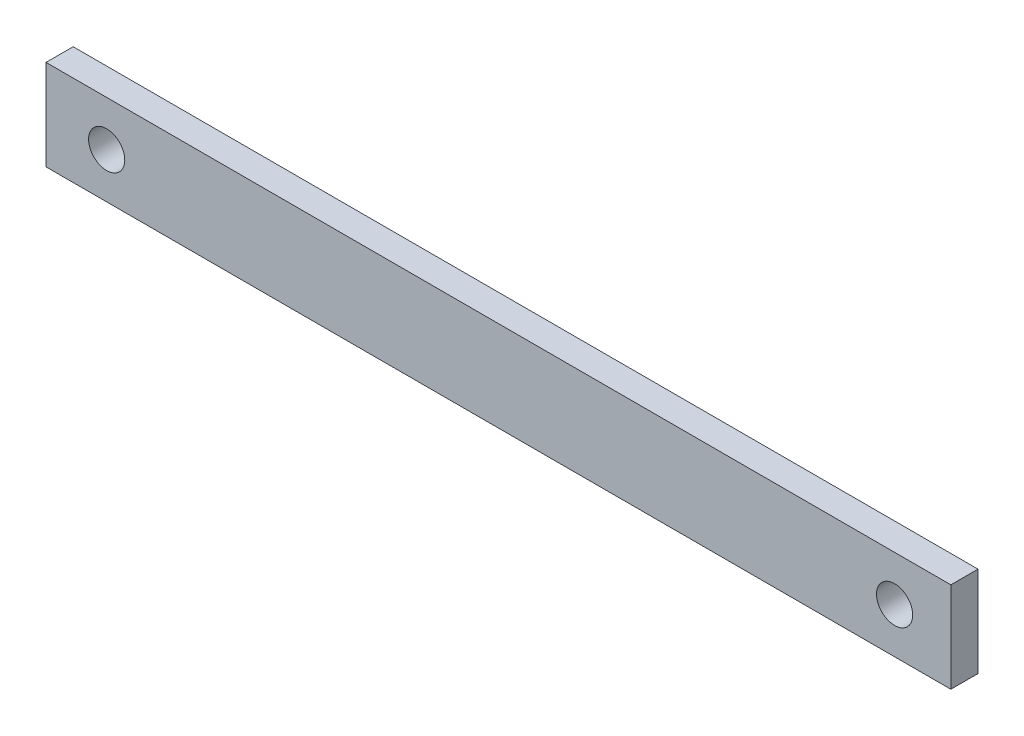
SolidWorks part; units mm, degrees
ref_plane "Front Plane" through (0, 0, 0) normal (0, 0, 1) x (1, 0, 0)
ref_plane "Top Plane" through (0, 0, 0) normal (0, 1, 0) x (1, 0, 0)
ref_plane "Right Plane" through (0, 0, 0) normal (1, 0, 0) x (0, 0, -1)
sketch "Sketch1" plane through (0, 0, 0) normal (0, 0, 1) x (1, 0, 0)
  line L1 (-50, 5) -> (50, 5)
  line L2 (-50, 5) -> (-50, -5)
  line L3 (-50, -5) -> (50, -5)
  line L4 (50, 5) -> (50, -5)
  line L5 (-50, 5) -> (50, -5) construction
  line L6 (-50, -5) -> (50, 5) construction
  point P0 (0, 0)
  dimension "D1" = 100
  dimension "D2" = 10
extrude "Boss-Extrude1" add sketch "Sketch1" along normal blind 3
sketch "Sketch2" plane through (0, 0, 3) normal (0, 0, 1) x (1, 0, 0)
  circle A0 centre (-43.2953, 0) radius 2
  circle A1 centre (43.7829, 0) radius 2
  point P4 (0, 0)
  dimension "D1" = 4
extrude "Cut-Extrude1" cut sketch "Sketch2" against normal blind 10
